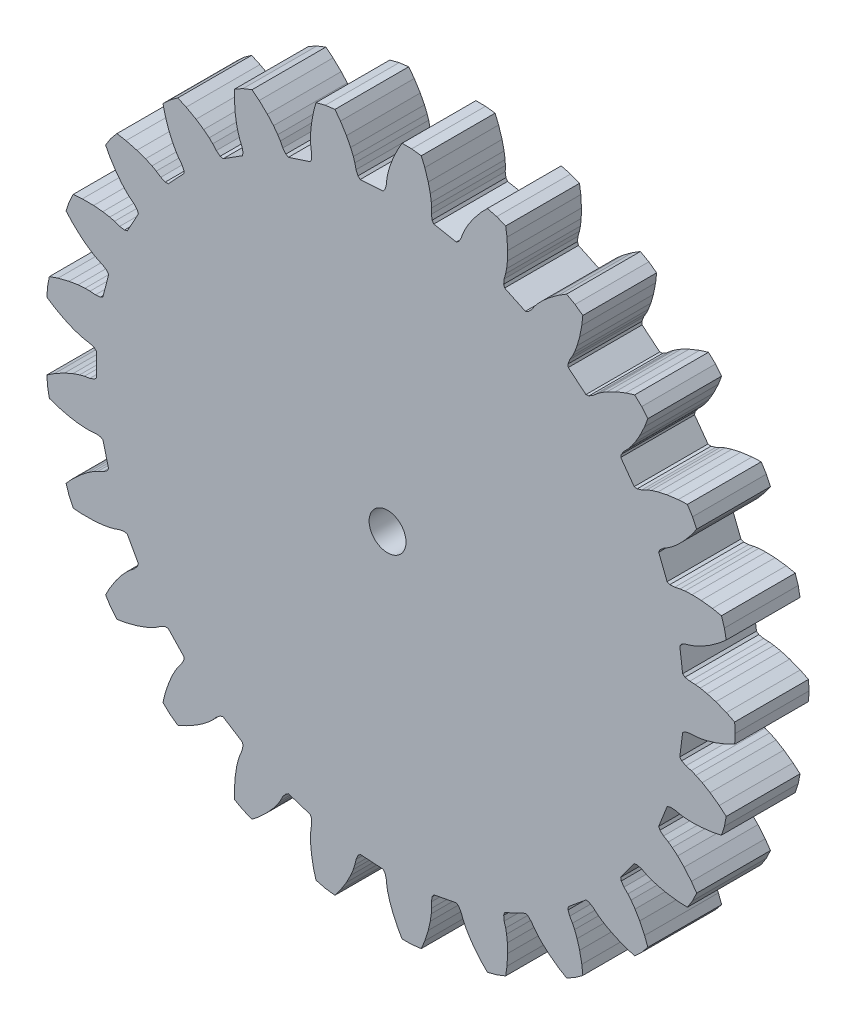
SolidWorks part; units mm, degrees
ref_plane "Front Plane" through (0, 0, 0) normal (0, 0, 1) x (1, 0, 0)
ref_plane "Top Plane" through (0, 0, 0) normal (0, 1, 0) x (1, 0, 0)
ref_plane "Right Plane" through (0, 0, 0) normal (1, 0, 0) x (0, 0, -1)
sketch "Model" plane through (0, 0, 0) normal (0, 0, 1) x (1, 0, 0)
  line L0 (28.7241, -8.2631) -> (28.9806, -7.4736)
  line L1 (28.9806, -7.4736) -> (29.1362, -6.6581)
  line L2 (29.1362, -6.6581) -> (28.5343, -6.1443)
  line L3 (28.5343, -6.1443) -> (27.7445, -5.5772)
  line L4 (27.7445, -5.5772) -> (27.0669, -5.172)
  line L5 (27.0669, -5.172) -> (26.5218, -4.9052)
  line L6 (26.5218, -4.9052) -> (26.1267, -4.7512)
  line L7 (26.1267, -4.7512) -> (25.6757, -4.6178)
  line L8 (25.6757, -4.6178) -> (25.3038, -4.4307)
  line L9 (25.3038, -4.4307) -> (25.1412, -4.2293)
  line L10 (25.1412, -4.2293) -> (25.388, -2.275)
  line L11 (25.388, -2.275) -> (25.5957, -2.1204)
  line L12 (25.5957, -2.1204) -> (26.0025, -2.0316)
  line L13 (26.0025, -2.0316) -> (26.4724, -2.0146)
  line L14 (26.4724, -2.0146) -> (26.8934, -1.9637)
  line L15 (26.8934, -1.9637) -> (27.4877, -1.8409)
  line L16 (27.4877, -1.8409) -> (28.2448, -1.6169)
  line L17 (28.2448, -1.6169) -> (29.1508, -1.264)
  line L18 (29.1508, -1.264) -> (29.8616, -0.916)
  line L19 (29.8616, -0.916) -> (29.9137, -0.0875)
  line L20 (29.9137, -0.0875) -> (29.8616, 0.7411)
  line L21 (29.8616, 0.7411) -> (29.1508, 1.089)
  line L22 (29.1508, 1.089) -> (28.2448, 1.4419)
  line L23 (28.2448, 1.4419) -> (27.4877, 1.6659)
  line L24 (27.4877, 1.6659) -> (26.8934, 1.7888)
  line L25 (26.8934, 1.7888) -> (26.4724, 1.8396)
  line L26 (26.4724, 1.8396) -> (26.0025, 1.8567)
  line L27 (26.0025, 1.8567) -> (25.5957, 1.9454)
  line L28 (25.5957, 1.9454) -> (25.388, 2.1)
  line L29 (25.388, 2.1) -> (25.1412, 4.0543)
  line L30 (25.1412, 4.0543) -> (25.3038, 4.2558)
  line L31 (25.3038, 4.2558) -> (25.6757, 4.4428)
  line L32 (25.6757, 4.4428) -> (26.1267, 4.5763)
  line L33 (26.1267, 4.5763) -> (26.5218, 4.7302)
  line L34 (26.5218, 4.7302) -> (27.0669, 4.997)
  line L35 (27.0669, 4.997) -> (27.7445, 5.4022)
  line L36 (27.7445, 5.4022) -> (28.5343, 5.9694)
  line L37 (28.5343, 5.9694) -> (29.1362, 6.4831)
  line L38 (29.1362, 6.4831) -> (28.9806, 7.2986)
  line L39 (28.9806, 7.2986) -> (28.7241, 8.0882)
  line L40 (28.7241, 8.0882) -> (27.9491, 8.2484)
  line L41 (27.9491, 8.2484) -> (26.9838, 8.3649)
  line L42 (26.9838, 8.3649) -> (26.1948, 8.3936)
  line L43 (26.1948, 8.3936) -> (25.5886, 8.3648)
  line L44 (25.5886, 8.3648) -> (25.1682, 8.3093)
  line L45 (25.1682, 8.3093) -> (24.7088, 8.209)
  line L46 (24.7088, 8.209) -> (24.2927, 8.1938)
  line L47 (24.2927, 8.1938) -> (24.0531, 8.2919)
  line L48 (24.0531, 8.2919) -> (23.328, 10.1234)
  line L49 (23.328, 10.1234) -> (23.4355, 10.359)
  line L50 (23.4355, 10.359) -> (23.7492, 10.6327)
  line L51 (23.7492, 10.6327) -> (24.1527, 10.874)
  line L52 (24.1527, 10.874) -> (24.4972, 11.1214)
  line L53 (24.4972, 11.1214) -> (24.9588, 11.5154)
  line L54 (24.9588, 11.5154) -> (25.5143, 12.0764)
  line L55 (25.5143, 12.0764) -> (26.1383, 12.8221)
  line L56 (26.1383, 12.8221) -> (26.5935, 13.4694)
  line L57 (26.5935, 13.4694) -> (26.24, 14.2206)
  line L58 (26.24, 14.2206) -> (25.7952, 14.9215)
  line L59 (25.7952, 14.9215) -> (25.0047, 14.884)
  line L60 (25.0047, 14.884) -> (24.0408, 14.7568)
  line L61 (24.0408, 14.7568) -> (23.2694, 14.5884)
  line L62 (23.2694, 14.5884) -> (22.6894, 14.4097)
  line L63 (22.6894, 14.4097) -> (22.296, 14.2514)
  line L64 (22.296, 14.2514) -> (21.876, 14.04)
  line L65 (21.876, 14.04) -> (21.4768, 13.9218)
  line L66 (21.4768, 13.9218) -> (21.2203, 13.9573)
  line L67 (21.2203, 13.9573) -> (20.0625, 15.5509)
  line L68 (20.0625, 15.5509) -> (20.108, 15.8058)
  line L69 (20.108, 15.8058) -> (20.3438, 16.1489)
  line L70 (20.3438, 16.1489) -> (20.6746, 16.483)
  line L71 (20.6746, 16.483) -> (20.9468, 16.8083)
  line L72 (20.9468, 16.8083) -> (21.2959, 17.3047)
  line L73 (21.2959, 17.3047) -> (21.6944, 17.9863)
  line L74 (21.6944, 17.9863) -> (22.1133, 18.8637)
  line L75 (22.1133, 18.8637) -> (22.3933, 19.6039)
  line L76 (22.3933, 19.6039) -> (21.8641, 20.2436)
  line L77 (21.8641, 20.2436) -> (21.2589, 20.8119)
  line L78 (21.2589, 20.8119) -> (20.5026, 20.5789)
  line L79 (20.5026, 20.5789) -> (19.6006, 20.216)
  line L80 (19.6006, 20.216) -> (18.8953, 19.861)
  line L81 (18.8953, 19.861) -> (18.378, 19.5438)
  line L82 (18.378, 19.5438) -> (18.0363, 19.2926)
  line L83 (18.0363, 19.2926) -> (17.682, 18.9833)
  line L84 (17.682, 18.9833) -> (17.3248, 18.7696)
  line L85 (17.3248, 18.7696) -> (17.0676, 18.7401)
  line L86 (17.0676, 18.7401) -> (15.5498, 19.9958)
  line L87 (15.5498, 19.9958) -> (15.5305, 20.254)
  line L88 (15.5305, 20.254) -> (15.6735, 20.645)
  line L89 (15.6735, 20.645) -> (15.9109, 21.0509)
  line L90 (15.9109, 21.0509) -> (16.0936, 21.4336)
  line L91 (16.0936, 21.4336) -> (16.3083, 22.0012)
  line L92 (16.3083, 22.0012) -> (16.5248, 22.7605)
  line L93 (16.5248, 22.7605) -> (16.7123, 23.7145)
  line L94 (16.7123, 23.7145) -> (16.7994, 24.5011)
  line L95 (16.7994, 24.5011) -> (16.1278, 24.9891)
  line L96 (16.1278, 24.9891) -> (15.4003, 25.389)
  line L97 (15.4003, 25.389) -> (14.7257, 24.9753)
  line L98 (14.7257, 24.9753) -> (13.9422, 24.3994)
  line L99 (13.9422, 24.3994) -> (13.3474, 23.8802)
  line L100 (13.3474, 23.8802) -> (12.9252, 23.4443)
  line L101 (12.9252, 23.4443) -> (12.6567, 23.116)
  line L102 (12.6567, 23.116) -> (12.3905, 22.7284)
  line L103 (12.3905, 22.7284) -> (12.0977, 22.4325)
  line L104 (12.0977, 22.4325) -> (11.8558, 22.34)
  line L105 (11.8558, 22.34) -> (10.0734, 23.1788)
  line L106 (10.0734, 23.1788) -> (9.9905, 23.424)
  line L107 (9.9905, 23.424) -> (10.0319, 23.8383)
  line L108 (10.0319, 23.8383) -> (10.1608, 24.2905)
  line L109 (10.1608, 24.2905) -> (10.2426, 24.7066)
  line L110 (10.2426, 24.7066) -> (10.3094, 25.3098)
  line L111 (10.3094, 25.3098) -> (10.3303, 26.0991)
  line L112 (10.3303, 26.0991) -> (10.2747, 27.0698)
  line L113 (10.2747, 27.0698) -> (10.1634, 27.8533)
  line L114 (10.1634, 27.8533) -> (9.3915, 28.1589)
  line L115 (9.3915, 28.1589) -> (8.5874, 28.3653)
  line L116 (8.5874, 28.3653) -> (8.0369, 27.7969)
  line L117 (8.0369, 27.7969) -> (7.4213, 27.0443)
  line L118 (7.4213, 27.0443) -> (6.9743, 26.3934)
  line L119 (6.9743, 26.3934) -> (6.6738, 25.8662)
  line L120 (6.6738, 25.8662) -> (6.4953, 25.4815)
  line L121 (6.4953, 25.4815) -> (6.3339, 25.0399)
  line L122 (6.3339, 25.0399) -> (6.1238, 24.6804)
  line L123 (6.1238, 24.6804) -> (5.9126, 24.5307)
  line L124 (5.9126, 24.5307) -> (3.9776, 24.8998)
  line L125 (3.9776, 24.8998) -> (3.8363, 25.1168)
  line L126 (3.8363, 25.1168) -> (3.7733, 25.5283)
  line L127 (3.7733, 25.5283) -> (3.7858, 25.9984)
  line L128 (3.7858, 25.9984) -> (3.7615, 26.4218)
  line L129 (3.7615, 26.4218) -> (3.6762, 27.0226)
  line L130 (3.6762, 27.0226) -> (3.5001, 27.7923)
  line L131 (3.5001, 27.7923) -> (3.2048, 28.7186)
  line L132 (3.2048, 28.7186) -> (2.9022, 29.4499)
  line L133 (2.9022, 29.4499) -> (2.0786, 29.5539)
  line L134 (2.0786, 29.5539) -> (1.2484, 29.5539)
  line L135 (1.2484, 29.5539) -> (0.8565, 28.8664)
  line L136 (0.8565, 28.8664) -> (0.4474, 27.9843)
  line L137 (0.4474, 27.9843) -> (0.1763, 27.2428)
  line L138 (0.1763, 27.2428) -> (0.0164, 26.6574)
  line L139 (0.0164, 26.6574) -> (-0.0608, 26.2404)
  line L140 (-0.0608, 26.2404) -> (-0.1073, 25.7725)
  line L141 (-0.1073, 25.7725) -> (-0.2214, 25.3721)
  line L142 (-0.2214, 25.3721) -> (-0.3888, 25.1745)
  line L143 (-0.3888, 25.1745) -> (-2.3547, 25.0508)
  line L144 (-2.3547, 25.0508) -> (-2.5456, 25.2258)
  line L145 (-2.5456, 25.2258) -> (-2.7089, 25.6088)
  line L146 (-2.7089, 25.6088) -> (-2.8138, 26.0672)
  line L147 (-2.8138, 26.0672) -> (-2.9426, 26.4712)
  line L148 (-2.9426, 26.4712) -> (-3.1746, 27.032)
  line L149 (-3.1746, 27.032) -> (-3.5365, 27.7337)
  line L150 (-3.5365, 27.7337) -> (-4.0529, 28.5575)
  line L151 (-4.0529, 28.5575) -> (-4.5279, 29.1905)
  line L152 (-4.5279, 29.1905) -> (-5.3515, 29.0864)
  line L153 (-5.3515, 29.0864) -> (-6.1556, 28.88)
  line L154 (-6.1556, 28.88) -> (-6.3642, 28.1166)
  line L155 (-6.3642, 28.1166) -> (-6.5411, 27.1605)
  line L156 (-6.5411, 27.1605) -> (-6.6193, 26.3749)
  line L157 (-6.6193, 26.3749) -> (-6.6286, 25.7681)
  line L158 (-6.6286, 25.7681) -> (-6.5996, 25.345)
  line L159 (-6.5996, 25.345) -> (-6.5283, 24.8802)
  line L160 (-6.5283, 24.8802) -> (-6.5393, 24.464)
  line L161 (-6.5393, 24.464) -> (-6.6522, 24.231)
  line L162 (-6.6522, 24.231) -> (-8.5257, 23.6223)
  line L163 (-8.5257, 23.6223) -> (-8.754, 23.7444)
  line L164 (-8.754, 23.7444) -> (-9.0075, 24.0747)
  line L165 (-9.0075, 24.0747) -> (-9.223, 24.4926)
  line L166 (-9.223, 24.4926) -> (-9.4483, 24.8519)
  line L167 (-9.4483, 24.8519) -> (-9.8125, 25.3373)
  line L168 (-9.8125, 25.3373) -> (-10.3376, 25.927)
  line L169 (-10.3376, 25.927) -> (-11.0426, 26.5965)
  line L170 (-11.0426, 26.5965) -> (-11.6601, 27.0915)
  line L171 (-11.6601, 27.0915) -> (-12.4319, 26.7859)
  line L172 (-12.4319, 26.7859) -> (-13.1594, 26.3859)
  line L173 (-13.1594, 26.3859) -> (-13.1716, 25.5947)
  line L174 (-13.1716, 25.5947) -> (-13.1052, 24.6247)
  line L175 (-13.1052, 24.6247) -> (-12.9855, 23.8442)
  line L176 (-12.9855, 23.8442) -> (-12.8437, 23.2542)
  line L177 (-12.8437, 23.2542) -> (-12.7104, 22.8516)
  line L178 (-12.7104, 22.8516) -> (-12.5257, 22.4191)
  line L179 (-12.5257, 22.4191) -> (-12.4328, 22.0133)
  line L180 (-12.4328, 22.0133) -> (-12.4843, 21.7595)
  line L181 (-12.4843, 21.7595) -> (-14.1475, 20.704)
  line L182 (-14.1475, 20.704) -> (-14.399, 20.7655)
  line L183 (-14.399, 20.7655) -> (-14.7267, 21.0223)
  line L184 (-14.7267, 21.0223) -> (-15.0394, 21.3735)
  line L185 (-15.0394, 21.3735) -> (-15.3469, 21.6656)
  line L186 (-15.3469, 21.6656) -> (-15.8204, 22.0451)
  line L187 (-15.8204, 22.0451) -> (-16.4756, 22.4857)
  line L188 (-16.4756, 22.4857) -> (-17.325, 22.9588)
  line L189 (-17.325, 22.9588) -> (-18.0462, 23.2847)
  line L190 (-18.0462, 23.2847) -> (-18.7178, 22.7968)
  line L191 (-18.7178, 22.7968) -> (-19.323, 22.2284)
  line L192 (-19.323, 22.2284) -> (-19.138, 21.459)
  line L193 (-19.138, 21.459) -> (-18.8324, 20.536)
  line L194 (-18.8324, 20.536) -> (-18.5224, 19.8098)
  line L195 (-18.5224, 19.8098) -> (-18.2383, 19.2736)
  line L196 (-18.2383, 19.2736) -> (-18.009, 18.9168)
  line L197 (-18.009, 18.9168) -> (-17.7227, 18.5438)
  line L198 (-17.7227, 18.5438) -> (-17.5317, 18.1739)
  line L199 (-17.5317, 18.1739) -> (-17.5185, 17.9153)
  line L200 (-17.5185, 17.9153) -> (-18.867, 16.4793)
  line L201 (-18.867, 16.4793) -> (-19.1259, 16.4763)
  line L202 (-19.1259, 16.4763) -> (-19.5071, 16.6436)
  line L203 (-19.5071, 16.6436) -> (-19.8973, 16.906)
  line L204 (-19.8973, 16.906) -> (-20.2678, 17.1124)
  line L205 (-20.2678, 17.1124) -> (-20.8208, 17.3623)
  line L206 (-20.8208, 17.3623) -> (-21.565, 17.6261)
  line L207 (-21.565, 17.6261) -> (-22.5054, 17.8731)
  line L208 (-22.5054, 17.8731) -> (-23.2849, 18.0094)
  line L209 (-23.2849, 18.0094) -> (-23.8141, 17.3697)
  line L210 (-23.8141, 17.3697) -> (-24.2589, 16.6688)
  line L211 (-24.2589, 16.6688) -> (-23.8884, 15.9695)
  line L212 (-23.8884, 15.9695) -> (-23.3629, 15.1515)
  line L213 (-23.3629, 15.1515) -> (-22.882, 14.5253)
  line L214 (-22.882, 14.5253) -> (-22.4735, 14.0765)
  line L215 (-22.4735, 14.0765) -> (-22.1627, 13.7879)
  line L216 (-22.1627, 13.7879) -> (-21.7926, 13.4979)
  line L217 (-21.7926, 13.4979) -> (-21.5157, 13.1871)
  line L218 (-21.5157, 13.1871) -> (-21.4385, 12.9399)
  line L219 (-21.4385, 12.9399) -> (-22.3875, 11.2137)
  line L220 (-22.3875, 11.2137) -> (-22.6375, 11.1464)
  line L221 (-22.6375, 11.1464) -> (-23.0484, 11.2136)
  line L222 (-23.0484, 11.2136) -> (-23.4916, 11.3707)
  line L223 (-23.4916, 11.3707) -> (-23.9018, 11.4785)
  line L224 (-23.9018, 11.4785) -> (-24.4996, 11.583)
  line L225 (-24.4996, 11.583) -> (-25.286, 11.6534)
  line L226 (-25.286, 11.6534) -> (-26.2583, 11.6588)
  line L227 (-26.2583, 11.6588) -> (-27.0472, 11.597)
  line L228 (-27.0472, 11.597) -> (-27.4007, 10.8458)
  line L229 (-27.4007, 10.8458) -> (-27.6572, 10.0563)
  line L230 (-27.6572, 10.0563) -> (-27.1244, 9.4711)
  line L231 (-27.1244, 9.4711) -> (-26.412, 8.8095)
  line L232 (-26.412, 8.8095) -> (-25.7905, 8.3225)
  line L233 (-25.7905, 8.3225) -> (-25.2832, 7.9895)
  line L234 (-25.2832, 7.9895) -> (-24.9104, 7.7872)
  line L235 (-24.9104, 7.7872) -> (-24.4798, 7.5984)
  line L236 (-24.4798, 7.5984) -> (-24.1342, 7.3661)
  line L237 (-24.1342, 7.3661) -> (-23.9981, 7.1459)
  line L238 (-23.9981, 7.1459) -> (-24.488, 5.2379)
  line L239 (-24.488, 5.2379) -> (-24.7134, 5.1106)
  line L240 (-24.7134, 5.1106) -> (-25.128, 5.0735)
  line L241 (-25.128, 5.0735) -> (-25.5964, 5.1155)
  line L242 (-25.5964, 5.1155) -> (-26.0205, 5.1178)
  line L243 (-26.0205, 5.1178) -> (-26.6255, 5.0704)
  line L244 (-26.6255, 5.0704) -> (-27.4047, 4.9431)
  line L245 (-27.4047, 4.9431) -> (-28.3478, 4.7065)
  line L246 (-28.3478, 4.7065) -> (-29.0965, 4.4504)
  line L247 (-29.0965, 4.4504) -> (-29.2521, 3.6349)
  line L248 (-29.2521, 3.6349) -> (-29.3042, 2.8064)
  line L249 (-29.3042, 2.8064) -> (-28.6427, 2.3721)
  line L250 (-28.6427, 2.3721) -> (-27.7881, 1.9084)
  line L251 (-27.7881, 1.9084) -> (-27.065, 1.5913)
  line L252 (-27.065, 1.5913) -> (-26.4908, 1.3949)
  line L253 (-26.4908, 1.3949) -> (-26.0794, 1.2917)
  line L254 (-26.0794, 1.2917) -> (-25.6154, 1.2159)
  line L255 (-25.6154, 1.2159) -> (-25.2229, 1.0769)
  line L256 (-25.2229, 1.0769) -> (-25.0363, 0.8974)
  line L257 (-25.0363, 0.8974) -> (-25.0363, -1.0724)
  line L258 (-25.0363, -1.0724) -> (-25.2229, -1.2519)
  line L259 (-25.2229, -1.2519) -> (-25.6154, -1.3909)
  line L260 (-25.6154, -1.3909) -> (-26.0794, -1.4667)
  line L261 (-26.0794, -1.4667) -> (-26.4908, -1.5699)
  line L262 (-26.4908, -1.5699) -> (-27.065, -1.7663)
  line L263 (-27.065, -1.7663) -> (-27.7881, -2.0834)
  line L264 (-27.7881, -2.0834) -> (-28.6427, -2.5471)
  line L265 (-28.6427, -2.5471) -> (-29.3042, -2.9813)
  line L266 (-29.3042, -2.9813) -> (-29.2521, -3.8099)
  line L267 (-29.2521, -3.8099) -> (-29.0965, -4.6254)
  line L268 (-29.0965, -4.6254) -> (-28.3478, -4.8815)
  line L269 (-28.3478, -4.8815) -> (-27.4047, -5.118)
  line L270 (-27.4047, -5.118) -> (-26.6255, -5.2454)
  line L271 (-26.6255, -5.2454) -> (-26.0205, -5.2928)
  line L272 (-26.0205, -5.2928) -> (-25.5964, -5.2904)
  line L273 (-25.5964, -5.2904) -> (-25.128, -5.2485)
  line L274 (-25.128, -5.2485) -> (-24.7134, -5.2855)
  line L275 (-24.7134, -5.2855) -> (-24.488, -5.4129)
  line L276 (-24.488, -5.4129) -> (-23.9981, -7.3209)
  line L277 (-23.9981, -7.3209) -> (-24.1342, -7.5411)
  line L278 (-24.1342, -7.5411) -> (-24.4798, -7.7733)
  line L279 (-24.4798, -7.7733) -> (-24.9104, -7.9622)
  line L280 (-24.9104, -7.9622) -> (-25.2832, -8.1645)
  line L281 (-25.2832, -8.1645) -> (-25.7905, -8.4975)
  line L282 (-25.7905, -8.4975) -> (-26.412, -8.9845)
  line L283 (-26.412, -8.9845) -> (-27.1244, -9.6461)
  line L284 (-27.1244, -9.6461) -> (-27.6572, -10.2312)
  line L570 (-27.6572, -10.2312) -> (-27.4007, -11.0208)
  line L571 (-27.4007, -11.0208) -> (-27.0472, -11.772)
  line L572 (-27.0472, -11.772) -> (-26.2583, -11.8338)
  line L573 (-26.2583, -11.8338) -> (-25.286, -11.8284)
  line L574 (-25.286, -11.8284) -> (-24.4996, -11.758)
  line L575 (-24.4996, -11.758) -> (-23.9018, -11.6534)
  line L576 (-23.9018, -11.6534) -> (-23.4916, -11.5457)
  line L577 (-23.4916, -11.5457) -> (-23.0484, -11.3886)
  line L578 (-23.0484, -11.3886) -> (-22.6375, -11.3213)
  line L579 (-22.6375, -11.3213) -> (-22.3875, -11.3887)
  line L580 (-22.3875, -11.3887) -> (-21.4385, -13.1149)
  line L581 (-21.4385, -13.1149) -> (-21.5157, -13.362)
  line L582 (-21.5157, -13.362) -> (-21.7926, -13.6729)
  line L583 (-21.7926, -13.6729) -> (-22.1627, -13.9629)
  line L584 (-22.1627, -13.9629) -> (-22.4735, -14.2515)
  line L585 (-22.4735, -14.2515) -> (-22.882, -14.7002)
  line L586 (-22.882, -14.7002) -> (-23.3629, -15.3265)
  line L587 (-23.3629, -15.3265) -> (-23.8884, -16.1445)
  line L588 (-23.8884, -16.1445) -> (-24.2589, -16.8438)
  line L589 (-24.2589, -16.8438) -> (-23.8141, -17.5447)
  line L590 (-23.8141, -17.5447) -> (-23.2849, -18.1844)
  line L591 (-23.2849, -18.1844) -> (-22.5054, -18.0481)
  line L592 (-22.5054, -18.0481) -> (-21.565, -17.8011)
  line L593 (-21.565, -17.8011) -> (-20.8208, -17.5373)
  line L594 (-20.8208, -17.5373) -> (-20.2678, -17.2874)
  line L595 (-20.2678, -17.2874) -> (-19.8973, -17.081)
  line L596 (-19.8973, -17.081) -> (-19.5071, -16.8186)
  line L597 (-19.5071, -16.8186) -> (-19.1259, -16.6513)
  line L598 (-19.1259, -16.6513) -> (-18.867, -16.6543)
  line L599 (-18.867, -16.6543) -> (-17.5185, -18.0903)
  line L600 (-17.5185, -18.0903) -> (-17.5317, -18.3489)
  line L601 (-17.5317, -18.3489) -> (-17.7227, -18.7188)
  line L602 (-17.7227, -18.7188) -> (-18.009, -19.0918)
  line L603 (-18.009, -19.0918) -> (-18.2383, -19.4486)
  line L604 (-18.2383, -19.4486) -> (-18.5224, -19.9848)
  line L605 (-18.5224, -19.9848) -> (-18.8324, -20.711)
  line L606 (-18.8324, -20.711) -> (-19.138, -21.634)
  line L607 (-19.138, -21.634) -> (-19.323, -22.4034)
  line L608 (-19.323, -22.4034) -> (-18.7178, -22.9717)
  line L609 (-18.7178, -22.9717) -> (-18.0462, -23.4597)
  line L610 (-18.0462, -23.4597) -> (-17.325, -23.1338)
  line L611 (-17.325, -23.1338) -> (-16.4756, -22.6607)
  line L612 (-16.4756, -22.6607) -> (-15.8204, -22.2201)
  line L613 (-15.8204, -22.2201) -> (-15.3469, -21.8405)
  line L614 (-15.3469, -21.8405) -> (-15.0394, -21.5485)
  line L615 (-15.0394, -21.5485) -> (-14.7267, -21.1973)
  line L616 (-14.7267, -21.1973) -> (-14.399, -20.9405)
  line L617 (-14.399, -20.9405) -> (-14.1475, -20.879)
  line L618 (-14.1475, -20.879) -> (-12.4843, -21.9345)
  line L619 (-12.4843, -21.9345) -> (-12.4328, -22.1883)
  line L620 (-12.4328, -22.1883) -> (-12.5257, -22.5941)
  line L621 (-12.5257, -22.5941) -> (-12.7104, -23.0265)
  line L622 (-12.7104, -23.0265) -> (-12.8437, -23.4292)
  line L623 (-12.8437, -23.4292) -> (-12.9855, -24.0192)
  line L624 (-12.9855, -24.0192) -> (-13.1052, -24.7996)
  line L625 (-13.1052, -24.7996) -> (-13.1716, -25.7696)
  line L626 (-13.1716, -25.7696) -> (-13.1594, -26.5609)
  line L627 (-13.1594, -26.5609) -> (-12.4319, -26.9609)
  line L628 (-12.4319, -26.9609) -> (-11.6601, -27.2665)
  line L629 (-11.6601, -27.2665) -> (-11.0426, -26.7715)
  line L630 (-11.0426, -26.7715) -> (-10.3376, -26.102)
  line L631 (-10.3376, -26.102) -> (-9.8125, -25.5123)
  line L632 (-9.8125, -25.5123) -> (-9.4483, -25.0269)
  line L633 (-9.4483, -25.0269) -> (-9.223, -24.6675)
  line L634 (-9.223, -24.6675) -> (-9.0075, -24.2496)
  line L635 (-9.0075, -24.2496) -> (-8.754, -23.9194)
  line L636 (-8.754, -23.9194) -> (-8.5257, -23.7973)
  line L637 (-8.5257, -23.7973) -> (-6.6522, -24.406)
  line L638 (-6.6522, -24.406) -> (-6.5393, -24.639)
  line L639 (-6.5393, -24.639) -> (-6.5283, -25.0552)
  line L640 (-6.5283, -25.0552) -> (-6.5996, -25.52)
  line L641 (-6.5996, -25.52) -> (-6.6286, -25.9431)
  line L642 (-6.6286, -25.9431) -> (-6.6193, -26.5498)
  line L643 (-6.6193, -26.5498) -> (-6.5411, -27.3355)
  line L644 (-6.5411, -27.3355) -> (-6.3642, -28.2916)
  line L645 (-6.3642, -28.2916) -> (-6.1556, -29.055)
  line L646 (-6.1556, -29.055) -> (-5.3515, -29.2614)
  line L647 (-5.3515, -29.2614) -> (-4.5279, -29.3655)
  line L648 (-4.5279, -29.3655) -> (-4.0529, -28.7325)
  line L649 (-4.0529, -28.7325) -> (-3.5365, -27.9087)
  line L650 (-3.5365, -27.9087) -> (-3.1746, -27.2069)
  line L651 (-3.1746, -27.2069) -> (-2.9426, -26.6462)
  line L652 (-2.9426, -26.6462) -> (-2.8138, -26.2421)
  line L653 (-2.8138, -26.2421) -> (-2.7089, -25.7838)
  line L654 (-2.7089, -25.7838) -> (-2.5456, -25.4008)
  line L655 (-2.5456, -25.4008) -> (-2.3547, -25.2258)
  line L656 (-2.3547, -25.2258) -> (-0.3888, -25.3495)
  line L657 (-0.3888, -25.3495) -> (-0.2214, -25.547)
  line L658 (-0.2214, -25.547) -> (-0.1073, -25.9474)
  line L659 (-0.1073, -25.9474) -> (-0.0608, -26.4153)
  line L660 (-0.0608, -26.4153) -> (0.0164, -26.8324)
  line L661 (0.0164, -26.8324) -> (0.1763, -27.4178)
  line L662 (0.1763, -27.4178) -> (0.4474, -28.1593)
  line L663 (0.4474, -28.1593) -> (0.8565, -29.0414)
  line L664 (0.8565, -29.0414) -> (1.2484, -29.7289)
  line L665 (1.2484, -29.7289) -> (2.0786, -29.7289)
  line L666 (2.0786, -29.7289) -> (2.9022, -29.6248)
  line L667 (2.9022, -29.6248) -> (3.2048, -28.8936)
  line L668 (3.2048, -28.8936) -> (3.5001, -27.9673)
  line L669 (3.5001, -27.9673) -> (3.6762, -27.1976)
  line L670 (3.6762, -27.1976) -> (3.7615, -26.5968)
  line L671 (3.7615, -26.5968) -> (3.7858, -26.1733)
  line L672 (3.7858, -26.1733) -> (3.7733, -25.7033)
  line L673 (3.7733, -25.7033) -> (3.8363, -25.2918)
  line L674 (3.8363, -25.2918) -> (3.9776, -25.0748)
  line L675 (3.9776, -25.0748) -> (5.9126, -24.7057)
  line L676 (5.9126, -24.7057) -> (6.1238, -24.8554)
  line L677 (6.1238, -24.8554) -> (6.3339, -25.2148)
  line L678 (6.3339, -25.2148) -> (6.4953, -25.6565)
  line L679 (6.4953, -25.6565) -> (6.6738, -26.0412)
  line L680 (6.6738, -26.0412) -> (6.9743, -26.5684)
  line L681 (6.9743, -26.5684) -> (7.4213, -27.2193)
  line L682 (7.4213, -27.2193) -> (8.0369, -27.9719)
  line L683 (8.0369, -27.9719) -> (8.5874, -28.5403)
  line L684 (8.5874, -28.5403) -> (9.3915, -28.3339)
  line L685 (9.3915, -28.3339) -> (10.1634, -28.0283)
  line L686 (10.1634, -28.0283) -> (10.2747, -27.2448)
  line L687 (10.2747, -27.2448) -> (10.3303, -26.2741)
  line L688 (10.3303, -26.2741) -> (10.3094, -25.4848)
  line L689 (10.3094, -25.4848) -> (10.2426, -24.8816)
  line L690 (10.2426, -24.8816) -> (10.1608, -24.4655)
  line L691 (10.1608, -24.4655) -> (10.0319, -24.0133)
  line L692 (10.0319, -24.0133) -> (9.9905, -23.599)
  line L693 (9.9905, -23.599) -> (10.0734, -23.3537)
  line L694 (10.0734, -23.3537) -> (11.8558, -22.515)
  line L695 (11.8558, -22.515) -> (12.0977, -22.6075)
  line L696 (12.0977, -22.6075) -> (12.3905, -22.9034)
  line L697 (12.3905, -22.9034) -> (12.6567, -23.291)
  line L698 (12.6567, -23.291) -> (12.9252, -23.6193)
  line L699 (12.9252, -23.6193) -> (13.3474, -24.0552)
  line L700 (13.3474, -24.0552) -> (13.9422, -24.5744)
  line L701 (13.9422, -24.5744) -> (14.7257, -25.1503)
  line L702 (14.7257, -25.1503) -> (15.4003, -25.564)
  line L703 (15.4003, -25.564) -> (16.1278, -25.164)
  line L704 (16.1278, -25.164) -> (16.7994, -24.6761)
  line L705 (16.7994, -24.6761) -> (16.7123, -23.8895)
  line L706 (16.7123, -23.8895) -> (16.5248, -22.9355)
  line L707 (16.5248, -22.9355) -> (16.3083, -22.1762)
  line L708 (16.3083, -22.1762) -> (16.0936, -21.6086)
  line L709 (16.0936, -21.6086) -> (15.9109, -21.2258)
  line L710 (15.9109, -21.2258) -> (15.6735, -20.8199)
  line L711 (15.6735, -20.8199) -> (15.5305, -20.429)
  line L712 (15.5305, -20.429) -> (15.5498, -20.1708)
  line L713 (15.5498, -20.1708) -> (17.0676, -18.9151)
  line L714 (17.0676, -18.9151) -> (17.3248, -18.9446)
  line L715 (17.3248, -18.9446) -> (17.682, -19.1583)
  line L716 (17.682, -19.1583) -> (18.0363, -19.4676)
  line L717 (18.0363, -19.4676) -> (18.378, -19.7187)
  line L718 (18.378, -19.7187) -> (18.8953, -20.036)
  line L719 (18.8953, -20.036) -> (19.6006, -20.391)
  line L720 (19.6006, -20.391) -> (20.5026, -20.7539)
  line L721 (20.5026, -20.7539) -> (21.2589, -20.9868)
  line L722 (21.2589, -20.9868) -> (21.8641, -20.4185)
  line L723 (21.8641, -20.4185) -> (22.3933, -19.7789)
  line L724 (22.3933, -19.7789) -> (22.1133, -19.0387)
  line L725 (22.1133, -19.0387) -> (21.6944, -18.1612)
  line L726 (21.6944, -18.1612) -> (21.2959, -17.4797)
  line L727 (21.2959, -17.4797) -> (20.9468, -16.9833)
  line L728 (20.9468, -16.9833) -> (20.6746, -16.658)
  line L729 (20.6746, -16.658) -> (20.3438, -16.3239)
  line L730 (20.3438, -16.3239) -> (20.108, -15.9808)
  line L731 (20.108, -15.9808) -> (20.0625, -15.7259)
  line L732 (20.0625, -15.7259) -> (21.2203, -14.1322)
  line L733 (21.2203, -14.1322) -> (21.4768, -14.0968)
  line L734 (21.4768, -14.0968) -> (21.876, -14.215)
  line L735 (21.876, -14.215) -> (22.296, -14.4264)
  line L736 (22.296, -14.4264) -> (22.6894, -14.5847)
  line L737 (22.6894, -14.5847) -> (23.2694, -14.7633)
  line L738 (23.2694, -14.7633) -> (24.0408, -14.9318)
  line L739 (24.0408, -14.9318) -> (25.0047, -15.059)
  line L740 (25.0047, -15.059) -> (25.7952, -15.0965)
  line L741 (25.7952, -15.0965) -> (26.24, -14.3956)
  line L742 (26.24, -14.3956) -> (26.5935, -13.6444)
  line L743 (26.5935, -13.6444) -> (26.1383, -12.9971)
  line L744 (26.1383, -12.9971) -> (25.5143, -12.2514)
  line L745 (25.5143, -12.2514) -> (24.9588, -11.6903)
  line L746 (24.9588, -11.6903) -> (24.4972, -11.2964)
  line L747 (24.4972, -11.2964) -> (24.1527, -11.049)
  line L748 (24.1527, -11.049) -> (23.7492, -10.8077)
  line L749 (23.7492, -10.8077) -> (23.4355, -10.5339)
  line L750 (23.4355, -10.5339) -> (23.328, -10.2984)
  line L751 (23.328, -10.2984) -> (24.0531, -8.4669)
  line L752 (24.0531, -8.4669) -> (24.2927, -8.3687)
  line L753 (24.2927, -8.3687) -> (24.7088, -8.384)
  line L754 (24.7088, -8.384) -> (25.1682, -8.4843)
  line L755 (25.1682, -8.4843) -> (25.5886, -8.5398)
  line L756 (25.5886, -8.5398) -> (26.1948, -8.5685)
  line L757 (26.1948, -8.5685) -> (26.9838, -8.5399)
  line L758 (26.9838, -8.5399) -> (27.9491, -8.4234)
  line L759 (27.9491, -8.4234) -> (28.7241, -8.2631)
  circle A0 centre (0, 0) radius 1.5875
  point P0 (0, 0)
  point P288 (0, 0)
  point P574 (0, 0)
  dimension "D1" = 3.175
extrude "Boss-Extrude1" add sketch "Model" along normal blind 6.35
